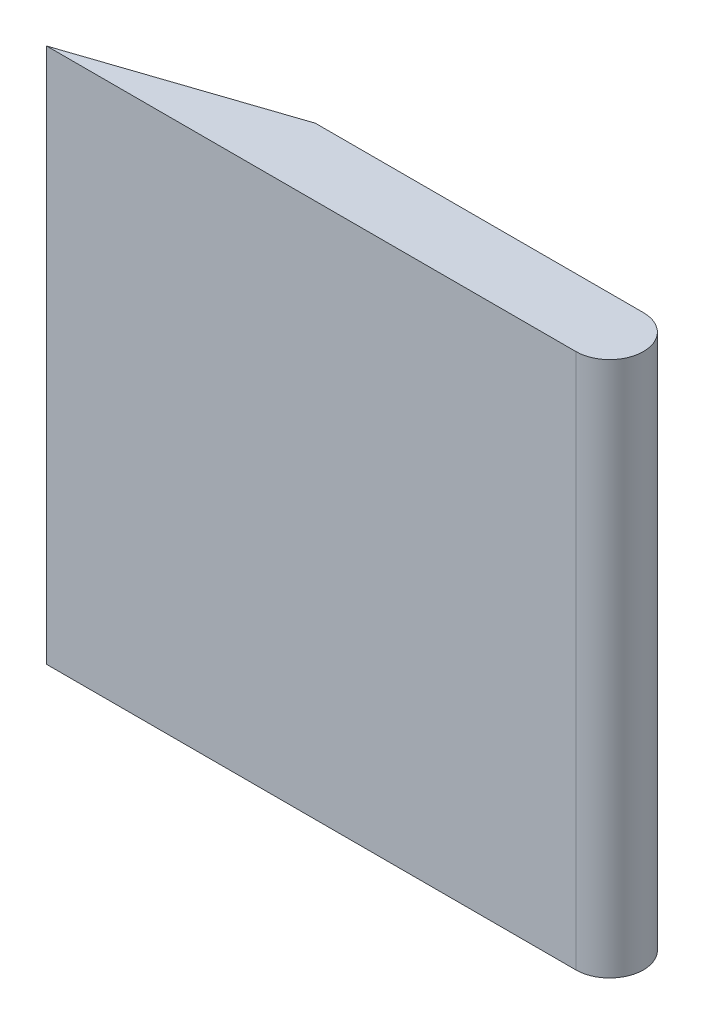
SolidWorks part; units mm, degrees
ref_plane "Front Plane" through (0, 0, 0) normal (0, 0, 1) x (1, 0, 0)
ref_plane "Top Plane" through (0, 0, 0) normal (0, 1, 0) x (1, 0, 0)
ref_plane "Right Plane" through (0, 0, 0) normal (1, 0, 0) x (0, 0, -1)
sketch "Sketch1" plane through (0, 0, 0) normal (0, 1, 0) x (1, 0, 0)
  line L0 (0, -0.8) -> (-12.55, -0.8)
  line L1 (0, 0.8) -> (-7.78, 0.8)
  line L2 (-7.78, 0.8) -> (-12.55, -0.8)
  arc A0 (0, 0.8) -> (0, -0.8) centre (0, 0) cw
  dimension "D1" = 0.8
  dimension "D2" = 12.55
  dimension "D3" = 7.78
extrude "Boss-Extrude1" add sketch "Sketch1" along normal blind 12.7
